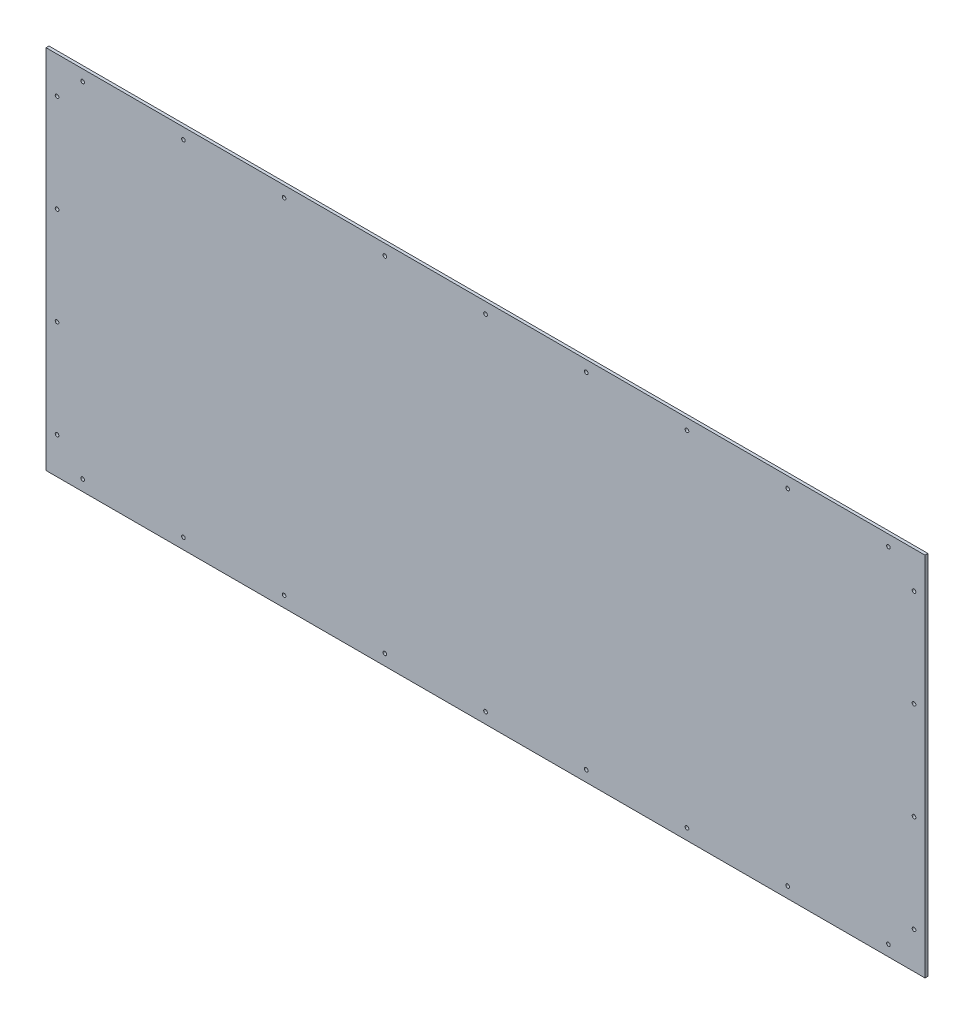
SolidWorks part; units mm, degrees
ref_plane "Alzado" through (0, 0, 0) normal (0, 0, 1) x (1, 0, 0)
ref_plane "Planta" through (0, 0, 0) normal (0, 1, 0) x (1, 0, 0)
ref_plane "Vista lateral" through (0, 0, 0) normal (1, 0, 0) x (0, 0, -1)
sketch "Croquis2" plane through (0, 0, 0) normal (0, 0, 1) x (1, 0, 0)
  line L1 (-300, -125) -> (300, -125)
  line L2 (-300, -125) -> (-300, 125)
  line L3 (-300, 125) -> (300, 125)
  line L4 (300, -125) -> (300, 125)
  line L5 (-300, -125) -> (300, 125) construction
  line L6 (-300, 125) -> (300, -125) construction
  point P0 (0, 0)
extrude "Saliente-Extruir1" add sketch "Croquis2" along normal blind 2
sketch "Croquis5" plane through (0, 0, 0) normal (0, 0, 1) x (1, 0, 0)
  line L223 (-300, 0) -> (-292.5, 0) construction
  line L224 (-300, 125) -> (-300, -125) construction
  line L225 (-292.5, -100) -> (-292.5, -33.3333) construction
  line L227 (-292.5, -33.3333) -> (-292.5, 33.3333) construction
  line L228 (-292.5, 117.5) -> (-292.5, 100) construction
  line L229 (-292.5, 33.3333) -> (-292.5, 100) construction
  line L230 (0, 125) -> (0, 112.4645) construction
  line L231 (292.5, 33.3333) -> (292.5, 100) construction
  line L232 (-292.5, 100) -> (-292.5, 117.5) construction
  line L233 (292.5, -33.3333) -> (292.5, 33.3333) construction
  line L234 (292.5, -100) -> (292.5, -33.3333) construction
  line L235 (300, 0) -> (292.5, 0) construction
  circle A52 centre (-292.5, 100) radius 1.25
  circle A58 centre (-292.5, -100) radius 1.25
  circle A59 centre (-292.5, 33.3333) radius 1.25
  circle A60 centre (-292.5, -33.3333) radius 1.25
  circle A61 centre (292.5, -33.3333) radius 1.25
  circle A62 centre (292.5, 33.3333) radius 1.25
  circle A63 centre (292.5, -100) radius 1.25
  circle A64 centre (292.5, 100) radius 1.25
  line B0 (-300, 125) -> (300, 125) construction
  line B1 (-292.5, 117.5) -> (292.5, 117.5) construction
  line B2 (-292.5, 117.5) -> (-275, 117.5) construction
  line B3 (-275, 117.5) -> (0, 117.5) construction
  line B4 (0, 117.5) -> (-137.5, 117.5) construction
  line B5 (-137.5, 117.5) -> (-275, 117.5) construction
  line B6 (-275, 117.5) -> (-206.25, 117.5) construction
  line B7 (-206.25, 117.5) -> (0, 117.5) construction
  line B8 (0, 117.5) -> (-137.5, 117.5) construction
  line B9 (-137.5, 117.5) -> (-68.75, 117.5) construction
  line B10 (137.5, 117.5) -> (68.75, 117.5) construction
  line B11 (275, 117.5) -> (206.25, 117.5) construction
  line B12 (137.5, 117.5) -> (275, 117.5) construction
  circle B13 centre (-275, 117.5) radius 1.25
  circle B14 centre (-206.25, 117.5) radius 1.25
  circle B15 centre (-137.5, 117.5) radius 1.25
  circle B16 centre (-68.75, 117.5) radius 1.25
  circle B17 centre (68.75, 117.5) radius 1.25
  circle B18 centre (137.5, 117.5) radius 1.25
  circle B19 centre (206.25, 117.5) radius 1.25
  circle B20 centre (275, 117.5) radius 1.25
  circle B21 centre (0, 117.5) radius 1.25
  line B22 (300, -125) -> (-300, -125) construction
  line B23 (292.5, -117.5) -> (-292.5, -117.5) construction
  line B24 (137.5, -117.5) -> (275, -117.5) construction
  line B25 (275, -117.5) -> (206.25, -117.5) construction
  line B26 (137.5, -117.5) -> (68.75, -117.5) construction
  line B27 (-137.5, -117.5) -> (-68.75, -117.5) construction
  line B28 (0, -117.5) -> (-137.5, -117.5) construction
  line B29 (-206.25, -117.5) -> (0, -117.5) construction
  line B30 (-275, -117.5) -> (-206.25, -117.5) construction
  line B31 (-137.5, -117.5) -> (-275, -117.5) construction
  line B32 (0, -117.5) -> (-137.5, -117.5) construction
  line B33 (-275, -117.5) -> (0, -117.5) construction
  circle B34 centre (0, -117.5) radius 1.25
  circle B35 centre (275, -117.5) radius 1.25
  circle B36 centre (206.25, -117.5) radius 1.25
  circle B37 centre (137.5, -117.5) radius 1.25
  circle B38 centre (68.75, -117.5) radius 1.25
  circle B39 centre (-68.75, -117.5) radius 1.25
  circle B40 centre (-137.5, -117.5) radius 1.25
  circle B41 centre (-206.25, -117.5) radius 1.25
  circle B42 centre (-275, -117.5) radius 1.25
sketch_block_instance "Bloque3-1"
sketch_block "Bloque3"
sketch_block_instance "Bloque4-1"
sketch_block "Bloque4"
extrude "Cortar-Extruir3" cut sketch "Croquis5" along normal through all
